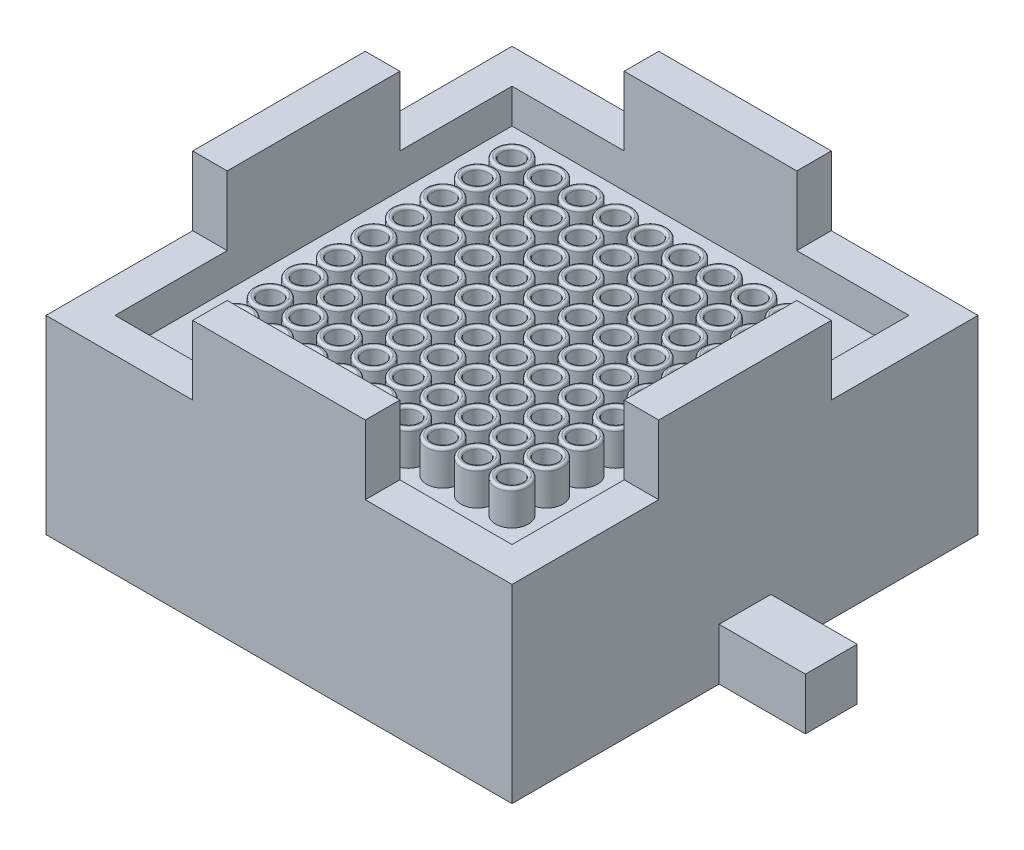
SolidWorks part; units mm, degrees
ref_plane "Front Plane" through (0, 0, 0) normal (0, 0, 1) x (1, 0, 0)
ref_plane "Top Plane" through (0, 0, 0) normal (0, 1, 0) x (1, 0, 0)
ref_plane "Right Plane" through (0, 0, 0) normal (1, 0, 0) x (0, 0, -1)
sketch "Sketch1" plane through (0, 0, 0) normal (0, 1, 0) x (1, 0, 0)
  line L0 (-13.5, 13.5) -> (13.5, 13.5)
  line L1 (-11.5, -11.5) -> (11.5, -11.5)
  line L2 (-11.5, -11.5) -> (-11.5, 11.5)
  line L3 (-11.5, 11.5) -> (11.5, 11.5)
  line L4 (11.5, -11.5) -> (11.5, 11.5)
  line L5 (-11.5, -11.5) -> (11.5, 11.5) construction
  line L6 (-11.5, 11.5) -> (11.5, -11.5) construction
  line L7 (13.5, -13.5) -> (13.5, 13.5)
  line L8 (-13.5, -13.5) -> (13.5, -13.5)
  line L9 (-13.5, -13.5) -> (-13.5, 13.5)
  point P0 (0, 0)
  dimension "D1" = 23
  dimension "D2" = 2
extrude "Boss-Extrude1" add sketch "Sketch1" along normal blind 2
sketch "Sketch2" plane through (0, 0, 0) normal (0, -1, 0) x (1, 0, 0)
  line L1 (-13.5, 13.5) -> (13.5, 13.5)
  line L2 (-13.5, 13.5) -> (-13.5, -13.5)
  line L3 (-13.5, -13.5) -> (13.5, -13.5)
  line L4 (13.5, 13.5) -> (13.5, -13.5)
  line L5 (-13.5, 13.5) -> (13.5, -13.5) construction
  line L6 (-13.5, -13.5) -> (13.5, 13.5) construction
  point P0 (0, 0)
extrude "Boss-Extrude2" add sketch "Sketch2" along normal blind 2
sketch "Sketch3" plane through (0, -2, 0) normal (0, -1, 0) x (1, 0, 0)
  line L0 (-11.5, 11.5) -> (11.5, 11.5)
  line L1 (-13.5, -13.5) -> (13.5, -13.5)
  line L2 (-13.5, -13.5) -> (-13.5, 13.5)
  line L3 (-13.5, 13.5) -> (13.5, 13.5)
  line L4 (13.5, -13.5) -> (13.5, 13.5)
  line L5 (-13.5, -13.5) -> (13.5, 13.5) construction
  line L6 (-13.5, 13.5) -> (13.5, -13.5) construction
  line L7 (11.5, -11.5) -> (11.5, 11.5)
  line L8 (-11.5, -11.5) -> (11.5, -11.5)
  line L9 (-11.5, -11.5) -> (-11.5, 11.5)
  point P0 (0, 0)
  dimension "D1" = 2
extrude "Boss-Extrude3" add sketch "Sketch3" along normal blind 5
sketch "Sketch6" plane through (0, 0, 0) normal (0, 1, 0) x (1, 0, 0)
  line L0 (11.5, -11.5) -> (11.5, 11.5) construction
  line L1 (11.5, 11.5) -> (-11.5, 11.5) construction
  circle A0 centre (8, 8) radius 0.95
  dimension "D2" = 1.9
  dimension "D1" = 3.5
  dimension "D3" = 3.5
extrude "Boss-Extrude5" add sketch "Sketch6" along normal blind 2
sketch "Sketch7" plane through (0, 2, 0) normal (0, 1, 0) x (1, 0, 0)
  circle A0 centre (8, 8) radius 0.625
  dimension "D1" = 1.25
extrude "Cut-Extrude2" cut sketch "Sketch7" against normal up to next (4 mm away)
fillet "Fillet3" radius 0.15 2 edges at (8, 2, -7.05) (8, 2, -7.375)
pattern_linear "LPattern1" count 9 spacing 2 along (0, 0, 1) count 9 spacing 2 along (-1, 0, 0) of "Boss-Extrude5", "Cut-Extrude2", "Fillet3"
sketch "Sketch11" plane through (0, -2, 0) normal (0, -1, 0) x (1, 0, 0)
  line L0 (11.5, 11.5) -> (-11.5, 11.5) construction
  line L1 (-11.5, 11.5) -> (-11.5, -11.5) construction
  circle A0 centre (-9, 9) radius 0.75
  dimension "D1" = 1.5
  dimension "D3" = 2.5
  dimension "D2" = 2.5
extrude "Boss-Extrude8" add sketch "Sketch11" along normal up to surface (5 mm away) up to face at (0, -7, 0)
pattern_linear "LPattern2" count 10 spacing 2 along (1, 0, 0) count 10 spacing 2 along (0, 0, -1) skipping (0, 1), (0, 3), (0, 5), (0, 7), (0, 9), (1, 0), (1, 2), (1, 4), (1, 6), (1, 8), (2, 1), (2, 3), (2, 5), (2, 7), (2, 9), (3, 0), (3, 2), (3, 4), (3, 6), (3, 8), (4, 1), (4, 3), (4, 5), (4, 7), (4, 9), (5, 0), (5, 2), (5, 4), (5, 6), (5, 8), (6, 1), (6, 3), (6, 5), (6, 7), (6, 9), (7, 0), (7, 2), (7, 4), (7, 6), (7, 8), (8, 1), (8, 3), (8, 5), (8, 7), (8, 9), (9, 0), (9, 2), (9, 4), (9, 6), (9, 8) of "Boss-Extrude8"
sketch "Sketch8" plane through (0, -7, 0) normal (0, -1, 0) x (1, 0, 0)
  line L1 (-13.5, -13.5) -> (13.5, -13.5)
  line L2 (-13.5, -13.5) -> (-13.5, 13.5)
  line L3 (-13.5, 13.5) -> (13.5, 13.5)
  line L4 (13.5, -13.5) -> (13.5, 13.5)
  line L5 (-13.5, -13.5) -> (13.5, 13.5) construction
  line L6 (-13.5, 13.5) -> (13.5, -13.5) construction
  point P0 (0, 0)
extrude "Boss-Extrude6" add sketch "Sketch8" along normal blind 2
sketch "Sketch9" plane through (0, -9, 0) normal (0, -1, 0) x (1, 0, 0)
  circle A0 centre (0, 0) radius 4.25
  dimension "D1" = 8.5
extrude "Cut-Extrude3" cut sketch "Sketch9" against normal blind 7
sketch "Sketch10" plane through (0, 2, 0) normal (0, 1, 0) x (1, 0, 0)
  line L0 (-13.5, 0) -> (-11.5, 0) construction
  line L1 (-13.5, 13.5) -> (-13.5, -13.5) construction
  line L2 (-11.5, 11.5) -> (-11.5, -11.5) construction
  line L4 (-11.5, 5) -> (-13.5, 5)
  line L5 (-11.5, 5) -> (-11.5, -5)
  line L6 (-11.5, -5) -> (-13.5, -5)
  line L7 (-13.5, 5) -> (-13.5, -5)
  line L8 (-11.5, 5) -> (-13.5, -5) construction
  line L9 (-11.5, -5) -> (-13.5, 5) construction
  point P6 (-12.5, 0)
  dimension "D1" = 10
extrude "Boss-Extrude7" add sketch "Sketch10" along normal blind 4
pattern_circular "CirPattern1" count 4 over 360 about axis through (0, 0, 0) along (0, 1, 0) of "Boss-Extrude7"
sketch "Sketch12" plane through (-13.5, 0, 0) normal (-1, 0, 0) x (0, 0, 1)
  line L0 (13.5, -9) -> (-13.5, -9) construction
  line L1 (1.5, -6) -> (-1.5, -6)
  line L2 (1.5, -6) -> (1.5, -9)
  line L3 (1.5, -9) -> (-1.5, -9)
  line L4 (-1.5, -6) -> (-1.5, -9)
  line L5 (1.5, -6) -> (-1.5, -9) construction
  line L6 (1.5, -9) -> (-1.5, -6) construction
  line L7 (0, 0) -> (0, -9) construction
  point P0 (0, -7.5)
  dimension "D1" = 3
extrude "Boss-Extrude9" add sketch "Sketch12" along normal blind 5
pattern_circular "CirPattern2" count 2 over 360 about axis through (0, 0, 0) along (0, 1, 0) of "Boss-Extrude9"
equation "\"D3@Sketch6\"=\"D1@Sketch6\""
equation "\"D3@Sketch11\"=\"D2@Sketch11\""
